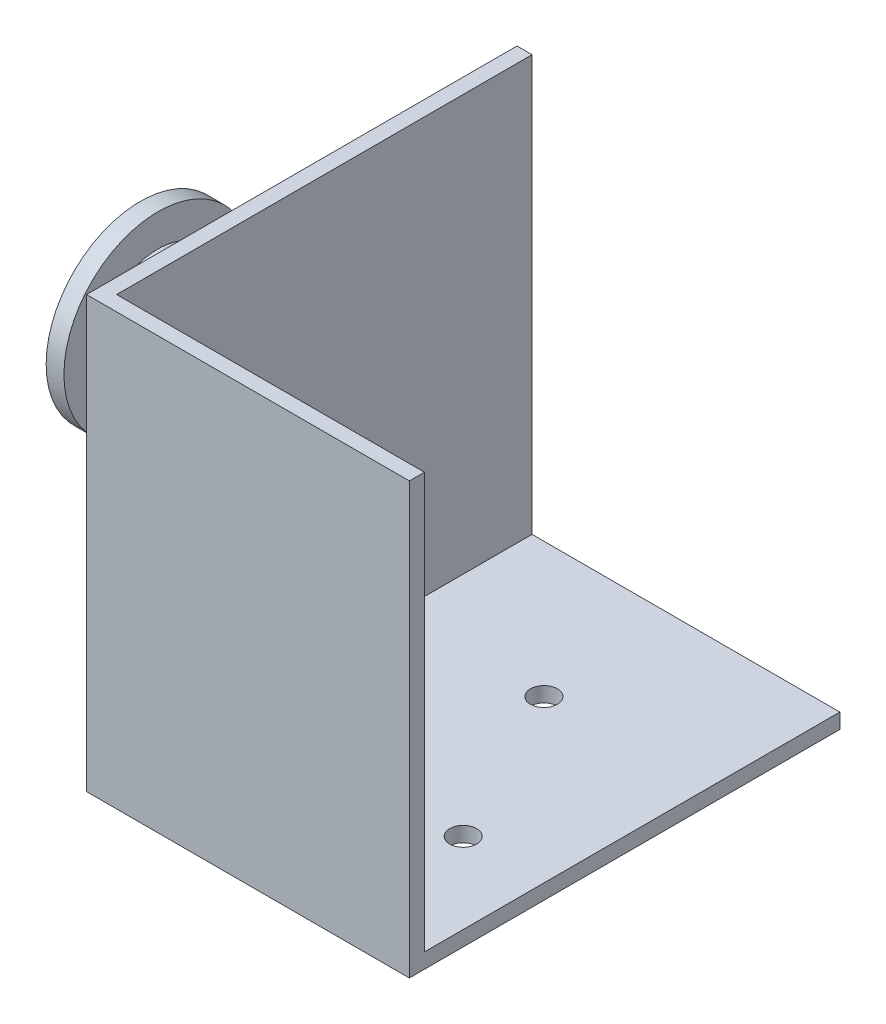
SolidWorks part; units mm, degrees
ref_plane "Front Plane" through (0, 0, 0) normal (0, 0, 1) x (1, 0, 0)
ref_plane "Top Plane" through (0, 0, 0) normal (0, 1, 0) x (1, 0, 0)
ref_plane "Right Plane" through (0, 0, 0) normal (1, 0, 0) x (0, 0, -1)
sketch "Sketch1" plane through (0, 0, 0) normal (0, 1, 0) x (1, 0, 0)
  line L1 (-15.24, 20.32) -> (15.24, 20.32)
  line L2 (-15.24, 20.32) -> (-15.24, -20.32)
  line L3 (-15.24, -20.32) -> (15.24, -20.32)
  line L4 (15.24, 20.32) -> (15.24, -20.32)
  point P4 (0, 0)
  point P5 (0, 0)
  point P6 (-15.24, 0)
  point P7 (0, 0)
  point P9 (0, 0)
  point P10 (0, 20.32)
  dimension "D1" = 30.48
  dimension "D2" = 40.64
extrude "Boss-Extrude1" add sketch "Sketch1" along normal mid plane 40.64
sketch "Sketch2" plane through (15.24, 0, 0) normal (1, 0, 0) x (0, 0, -1)
  line L3 (-18.8976, 20.32) -> (20.32, 20.32)
  line L4 (20.32, 20.32) -> (20.32, -18.8976)
  line L5 (-18.8976, -18.8976) -> (20.32, -18.8976)
  line L6 (-18.8976, 20.32) -> (-18.8976, -18.8976)
  line L7 (-18.8976, -18.8976) -> (20.32, -18.8976)
  line L8 (-18.8976, 20.32) -> (-18.8976, -18.8976)
  dimension "D1" = 1.4224
extrude "Cut-Extrude1" cut sketch "Sketch2" against normal offset from surface (29.0576 mm away) 1.4224 up to face at (-15.24, 0, 0)
sketch "Sketch3" plane through (0, -18.8976, 0) normal (0, 1, 0) x (1, 0, 0)
  line L0 (-13.8176, 20.32) -> (15.24, 20.32) construction
  line L1 (15.24, -18.8976) -> (15.24, 20.32) construction
  line L2 (-15.24, -20.32) -> (15.24, -20.32) construction
  circle A0 centre (-5.08, -7.62) radius 1.27
  circle A1 centre (7.62, -7.62) radius 1.27
  circle A2 centre (0, 7.62) radius 1.27
  point P8 (0, 0)
  point P10 (0, 0)
  dimension "D1" = 2.54
  dimension "D2" = 12.7
  dimension "D3" = 7.62
  dimension "D4" = 12.7
  dimension "D5" = 12.7
extrude "Cut-Extrude2" cut sketch "Sketch3" against normal through all
sketch "Sketch4" plane through (-15.24, 0, 0) normal (-1, 0, 0) x (0, 0, 1)
  line L0 (-20.32, -20.32) -> (20.32, -20.32) construction
  circle A0 centre (0, 1.27) radius 3.81
  dimension "D1" = 7.62
  dimension "D2" = 21.59
extrude "Boss-Extrude2" add sketch "Sketch4" along normal blind 19.05 contours A0
ref_plane "Plane1" through (0, 0, 0) normal (0, 0, 1) x (1, 0, 0)
sketch "Sketch5" plane through (0, 0, 0) normal (0, 0, 1) x (1, 0, 0)
  line L0 (-30.48, 5.08) -> (-30.48, 10.16)
  line L1 (-15.24, 5.08) -> (-34.29, 5.08) construction
  line L2 (-30.48, 10.16) -> (-28.8036, 10.16)
  line L3 (-28.8036, 10.16) -> (-28.8036, 7.112)
  line L4 (-28.8036, 7.112) -> (-21.8186, 7.112)
  line L5 (-21.8186, 7.112) -> (-21.8186, 10.16)
  line L6 (-21.8186, 10.16) -> (-20.1422, 10.16)
  line L7 (-20.1422, 10.16) -> (-20.1422, 5.08)
  line L8 (-20.1422, 5.08) -> (-30.48, 5.08)
  line L9 (-34.29, 1.27) -> (-15.24, 1.27) construction
  line L10 (-34.29, 5.08) -> (-34.29, -2.54) construction
  dimension "D1" = 1.6764
  dimension "D2" = 6.985
  dimension "D3" = 8.89
  dimension "D4" = 3.048
  dimension "D5" = 3.81
ref_axis "Axis1" through (-34.29, 1.27, 0) along (1, 0, 0)
revolve "Revolve1" add sketch "Sketch5" angle 360 about axis through (-34.29, 1.27, 0) along (1, 0, 0)
fillet "Fillet1" radius 2.54 1 edges at (-34.29, 1.27, 3.81)
